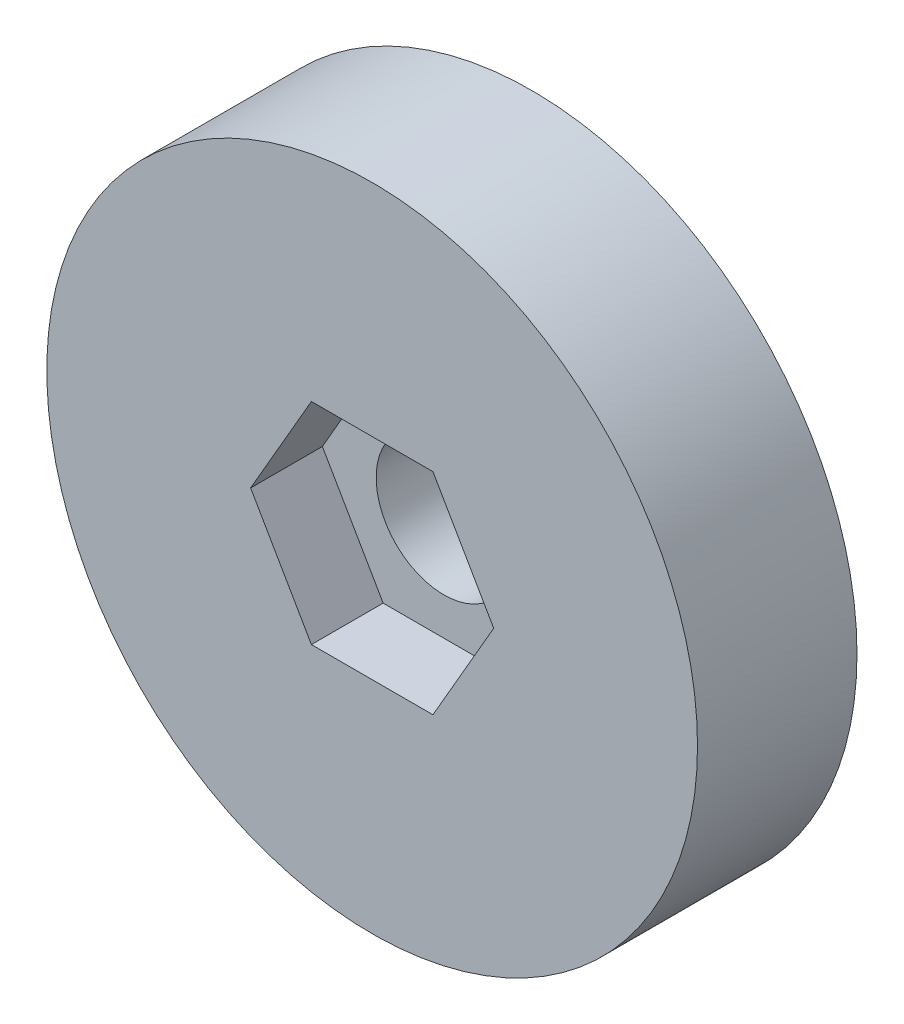
SolidWorks part; units mm, degrees
ref_plane "Plano frontal" through (0, 0, 0) normal (0, 0, 1) x (1, 0, 0)
ref_plane "Plano superior" through (0, 0, 0) normal (0, 1, 0) x (1, 0, 0)
ref_plane "Plano direito" through (0, 0, 0) normal (1, 0, 0) x (0, 0, -1)
sketch "Esboço1" plane through (0, 0, 0) normal (0, 0, 1) x (1, 0, 0)
  circle A0 centre (0, 0) radius 20.4
  circle A1 centre (0, 0) radius 4.25
extrude "Ressalto-extrusão1" add sketch "Esboço1" along normal blind 10
sketch "Esboço2" plane through (0, 0, 10) normal (0, 0, 1) x (1, 0, 0)
  line L1 (3.8105, -6.6) -> (7.621, 0)
  line L2 (7.621, 0) -> (3.8105, 6.6)
  line L3 (3.8105, 6.6) -> (-3.8105, 6.6)
  line L4 (-3.8105, 6.6) -> (-7.621, 0)
  line L5 (-7.621, 0) -> (-3.8105, -6.6)
  line L6 (-3.8105, -6.6) -> (3.8105, -6.6)
  circle A0 centre (0, 0) radius 6.6 construction
extrude "Corte-extrusão1" cut sketch "Esboço2" against normal blind 4.5
